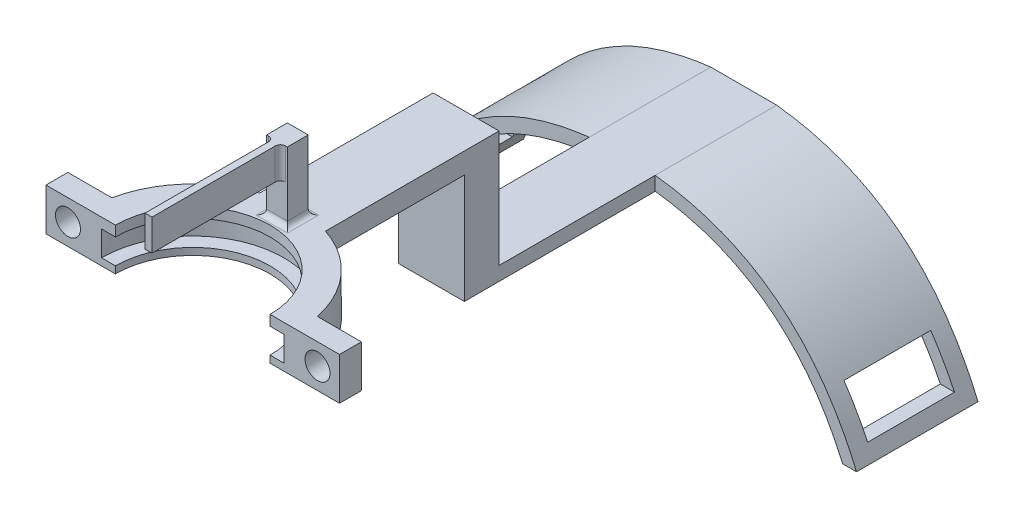
SolidWorks part; units mm, degrees
ref_plane "Front Plane" through (0, 0, 0) normal (0, 0, 1) x (1, 0, 0)
ref_plane "Top Plane" through (0, 0, 0) normal (0, 1, 0) x (1, 0, 0)
ref_plane "Right Plane" through (0, 0, 0) normal (1, 0, 0) x (0, 0, -1)
sketch "Sketch3" plane through (0, 0, 0) normal (0, 0, 1) x (1, 0, 0)
  line L2 (-62.6943, 11.7337) -> (-64.8845, 11.7337)
  line L3 (-62.8845, 10.2507) -> (-60.8845, 10.2507)
  line L5 (-60.8845, 6.6507) -> (-62.8845, 6.6507)
  line L6 (-62.8845, 6.6507) -> (-62.8845, 10.2507)
  line L10 (-64.8845, 11.7337) -> (-64.8845, 5.6398)
  line L11 (-64.8845, 5.6398) -> (-60.8845, 5.6398)
  line L12 (-60.8845, 5.6398) -> (-60.8845, 6.6507)
  line L13 (-60.8845, 10.2507) -> (-60.8845, 11.7337)
  line L14 (-60.8845, 11.7337) -> (-62.6943, 11.7337)
  dimension "D2" = 2
  dimension "D3" = 4
  dimension "D1" = 2
sketch "Sketch4" plane through (0, 0, 0) normal (0, 0, 1) x (1, 0, 0)
  line L0 (-49.7443, 0) -> (-49.7443, 12.8648) construction
  line L1 (27.6543, 0) -> (-27.6543, 0) construction
revolve "Revolve1" add sketch "Sketch3" angle 360 about L0
sketch "Sketch7" plane through (0, 11.7337, 0) normal (0, 1, 0) x (1, 0, 0)
  line L2 (-50.2443, 15.132) -> (-50.2443, 13.1308)
  line L3 (-49.2443, 15.132) -> (-49.2443, 13.1308)
  circle A0 centre (-49.7443, 0) radius 15.1403 construction
  arc A1 (-49.2443, 15.132) -> (-50.2443, 15.132) centre (-49.7443, 0) ccw
  circle A2 centre (-49.7443, 0) radius 13.1403 construction
  arc A3 (-49.2443, 13.1308) -> (-50.2443, 13.1308) centre (-49.7443, 0) ccw
  point P9 (-49.7443, 14.131)
  dimension "D1" = 1
extrude "Boss-Extrude1" add sketch "Sketch7" along normal blind 8.5
sketch "Sketch8" plane through (0, 20.2337, 0) normal (0, 1, 0) x (1, 0, 0)
  line L0 (-50.2443, 15.132) -> (-50.2443, 13.1308) construction
  line L3 (-50.2443, 15.132) -> (-50.2443, 13.1308)
  line L4 (-49.2443, 13.1308) -> (-49.2443, 15.132) construction
  line L5 (-49.2443, 13.1308) -> (-49.2443, 15.132)
  line L6 (-50.2443, 13.1308) -> (-50.2443, -6.3692)
  line L7 (-50.2443, -6.3692) -> (-49.2443, -6.3692)
  line L8 (-49.2443, -6.3692) -> (-49.2443, 13.1308)
  arc A0 (-49.2443, 15.132) -> (-50.2443, 15.132) centre (-49.7443, 0) ccw construction
  arc A1 (-49.2443, 15.132) -> (-50.2443, 15.132) centre (-49.7443, 0) ccw
  dimension "D1" = 19.5
extrude "Boss-Extrude2" add sketch "Sketch8" against normal blind 3
sketch "Sketch9" plane through (0, 11.7337, 0) normal (0, 1, 0) x (1, 0, 0)
  line L2 (-54.4943, 14.3759) -> (-54.4943, 39.3759)
  line L3 (-54.4943, 39.3759) -> (-44.9943, 39.3759)
  line L4 (-44.9943, 39.3759) -> (-44.9943, 14.3759)
  arc A0 (-50.2443, 15.132) -> (-49.2443, 15.132) centre (-49.7443, 0) ccw construction
  arc A1 (-50.2443, 15.132) -> (-54.4943, 14.3759) centre (-49.7443, 0) ccw
  arc A2 (-49.2443, 15.132) -> (-50.2443, 15.132) centre (-49.7443, 0) ccw construction
  arc A3 (-49.2443, 15.132) -> (-50.2443, 15.132) centre (-49.7443, 0) ccw
  arc A4 (-44.9943, 14.3759) -> (-49.2443, 15.132) centre (-49.7443, 0) ccw
  point P9 (-49.7443, 0)
  dimension "D1" = 25
extrude "Boss-Extrude3" add sketch "Sketch9" against normal blind 3
sketch "Sketch10" plane through (0, 8.7337, 0) normal (0, -1, 0) x (1, 0, 0)
  line L0 (-44.9943, -14.3759) -> (-44.9943, -39.3759) construction
  line L1 (-54.4943, -39.3759) -> (-44.9943, -39.3759)
  line L2 (-54.4943, -39.3759) -> (-54.4943, -34.3759)
  line L3 (-54.4943, -34.3759) -> (-44.9943, -34.3759)
  line L4 (-44.9943, -39.3759) -> (-44.9943, -34.3759)
  dimension "D1" = 5
extrude "Boss-Extrude4" add sketch "Sketch10" along normal blind 15.78
sketch "Sketch11" plane through (0, 0, -39.3759) normal (0, 0, -1) x (-1, 0, 0)
  line L0 (54.4943, -7.0463) -> (54.4943, 11.7337) construction
  line L1 (44.9943, -7.0463) -> (54.4943, -7.0463)
  line L2 (44.9943, -7.0463) -> (44.9943, -5.0463)
  line L3 (44.9943, -5.0463) -> (54.4943, -5.0463)
  line L4 (54.4943, -7.0463) -> (54.4943, -5.0463)
  dimension "D1" = 2
extrude "Boss-Extrude5" add sketch "Sketch11" along normal blind 40
sketch "Sketch13" plane through (0, 11.7337, 0) normal (0, 1, 0) x (1, 0, 0)
  line L2 (-49.7443, 3.15) -> (-49.7443, -3.15) construction
  line L3 (-28.604, 3.15) -> (-34.9353, 3.15)
  line L4 (-70.8845, 3.15) -> (-70.8845, -3.15)
  line L5 (-70.8845, -3.15) -> (-64.5532, -3.15)
  line L6 (-28.604, -3.15) -> (-28.604, 3.15)
  line L7 (-64.5532, 3.15) -> (-70.8845, 3.15)
  line L8 (-34.9353, -3.15) -> (-28.604, -3.15)
  arc A0 (-54.4943, 14.3759) -> (-44.9943, 14.3759) centre (-49.7443, 0) ccw construction
  arc A1 (-64.5532, 3.15) -> (-64.5532, -3.15) centre (-49.7443, 0) ccw
  arc A2 (-34.9353, -3.15) -> (-34.9353, 3.15) centre (-49.7443, 0) ccw
  point P10 (-49.7443, 0)
  point P13 (-49.7443, 3.15)
  dimension "D1" = 6.3
  dimension "D2" = 6.3
extrude "Boss-Extrude6" add sketch "Sketch13" against normal up to surface (6.0939 mm away) up to face at (-49.7443, 5.6398, -11.1403)
sketch "Sketch14" plane through (0, 0, 3.15) normal (0, 0, 1) x (1, 0, 0)
  line L0 (-70.8845, 11.7337) -> (-64.5532, 5.6398) construction
  line L1 (-28.604, 11.7337) -> (-34.9353, 5.6398) construction
  circle A0 centre (-31.7697, 8.6868) radius 1.8
  circle A1 centre (-67.7189, 8.6868) radius 1.8
  dimension "D1" = 3.6
  dimension "D2" = 3.6
extrude "Cut-Extrude1" cut sketch "Sketch14" against normal up to surface (6.3 mm away) contours A1 | A0 up to face at (-67.7189, 8.6868, -3.15)
sketch "Sketch15" plane through (0, 11.7337, 0) normal (0, 1, 0) x (1, 0, 0)
  line L0 (-70.8845, 0) -> (-23.4421, 0) construction
  line L1 (-70.8845, 3.15) -> (-70.8845, -3.15) construction
  line L2 (-15.004, 0) -> (15.004, 0) construction
  line L4 (-23.4421, 0) -> (-74.5953, 0)
  line L5 (-23.4421, 0) -> (-23.4421, -21.2106)
  line L6 (-23.4421, -21.2106) -> (-74.5953, -21.2106)
  line L7 (-74.5953, 0) -> (-74.5953, -21.2106)
extrude "Cut-Extrude3" cut sketch "Sketch15" against normal through all
sketch "Sketch16" plane through (0, 0, 0) normal (0, 1, 0) x (1, 0, 0)
  line L1 (-54.8883, 5.4174) -> (-45.2843, 5.4174)
  line L2 (-54.8883, 5.4174) -> (-54.8883, -6.4675)
  line L3 (-54.8883, -6.4675) -> (-45.2843, -6.4675)
  line L4 (-45.2843, 5.4174) -> (-45.2843, -6.4675)
sketch "Sketch18" plane through (0, 11.7337, 0) normal (0, 1, 0) x (1, 0, 0)
  line L0 (-50.2443, 15.132) -> (-49.2443, 15.132) construction
  line L1 (-48.2443, 15.132) -> (-51.2443, 15.132)
  line L2 (-51.2443, 15.132) -> (-51.2443, 12.132)
  line L3 (-51.2443, 12.132) -> (-48.2443, 12.132)
  line L4 (-48.2443, 12.132) -> (-48.2443, 15.132)
  point P7 (-49.7443, 15.132)
  dimension "D1" = 3
  dimension "D2" = 3
extrude "Boss-Extrude7" add sketch "Sketch18" along normal up to surface (8.5 mm away)
fillet "Fillet1" radius 0.75 6 edges at (-50.7443, 11.7337, -15.132) (-48.7443, 11.7337, -15.132) (-49.7443, 11.7337, -12.132) (-48.2443, 11.7337, -13.632) (-51.2443, 11.7337, -13.632) (-49.7443, 11.7337, -15.1403)
sketch "Sketch19" plane through (0, 20.2337, 0) normal (0, 1, 0) x (1, 0, 0)
  line L18 (-50.2443, 15.132) -> (-51.2443, 15.132)
  line L19 (-51.2443, 15.132) -> (-51.2443, 12.132)
  line L20 (-51.2443, 12.132) -> (-50.2443, 12.132)
  line L21 (-50.2443, 12.132) -> (-50.2443, -6.3692)
  line L22 (-50.2443, -6.3692) -> (-49.2443, -6.3692)
  line L23 (-49.2443, -6.3692) -> (-49.2443, 12.132)
  line L24 (-49.2443, 12.132) -> (-48.2443, 12.132)
  line L25 (-48.2443, 12.132) -> (-48.2443, 15.132)
  line L26 (-48.2443, 15.132) -> (-49.2443, 15.132)
  line L27 (-50.2443, 15.132) -> (-51.2443, 15.132)
  line L28 (-51.2443, 15.132) -> (-51.2443, 12.132)
  line L29 (-51.2443, 12.132) -> (-50.2443, 12.132)
  line L30 (-50.2443, 12.132) -> (-50.2443, -6.3692)
  line L31 (-50.2443, -6.3692) -> (-49.2443, -6.3692)
  line L32 (-49.2443, -6.3692) -> (-49.2443, 12.132)
  line L33 (-49.2443, 12.132) -> (-48.2443, 12.132)
  line L34 (-48.2443, 12.132) -> (-48.2443, 15.132)
  line L35 (-48.2443, 15.132) -> (-49.2443, 15.132)
  arc A2 (-49.2443, 15.132) -> (-50.2443, 15.132) centre (-49.7443, 0) ccw
  arc A3 (-49.2443, 15.132) -> (-50.2443, 15.132) centre (-49.7443, 0) ccw
  dimension "D1" = 0
extrude "Boss-Extrude8" add sketch "Sketch19" along normal blind 1.5
fillet "Fillet2" radius 0.75 2 edges at (-49.2443, 19.4837, -12.132) (-50.2443, 19.4837, -12.132)
sketch "Sketch20" plane through (0, 0, -79.3759) normal (0, 0, -1) x (-1, 0, 0)
  line L0 (49.7443, -5.0463) -> (49.7443, -27.5463) construction
  line L1 (54.4943, -5.0463) -> (44.9943, -5.0463) construction
  line L2 (83.4943, -27.5463) -> (15.9943, -27.5463) construction
  line L4 (15.9943, -27.5463) -> (17.9943, -27.5463)
  line L5 (81.4943, -27.5463) -> (83.4943, -27.5463)
  line L8 (44.9943, -7.0463) -> (54.4943, -7.0463)
  line L9 (44.9943, -5.0463) -> (54.4943, -5.0463)
  line L11 (54.4943, -5.0463) -> (44.9943, -5.0463) construction
  spline S0 degree 2 poles (15.9943, -27.5463) (24.4754, -7.3884) (44.9943, -5.0463) knots 0 0 0 0.448315 0.448315 0.448315
  spline S1 degree 2 poles (17.9943, -27.5463) (25.8778, -9.3271) (44.9943, -7.0463) knots 0 0 0 0.444959 0.444959 0.444959
  spline S2 degree 2 poles (54.4943, -5.0463) (75.0132, -7.3884) (83.4943, -27.5463) knots 0.551685 0.551685 0.551685 1 1 1
  spline S3 degree 2 poles (54.4943, -7.0463) (73.6108, -9.3271) (81.4943, -27.5463) knots 0.555041 0.555041 0.555041 1 1 1
  point P7 (49.7443, -27.5463)
  dimension "D3" = 2
  dimension "D1" = 22.5
  dimension "D2" = 67.5
  dimension "D4" = 2
extrude "Boss-Extrude9" add sketch "Sketch20" against normal blind 17.5
sketch "Sketch21" plane through (-44.9943, 0, 0) normal (1, 0, 0) x (0, 0, -1)
  line L0 (70.6259, -27.5463) -> (70.6259, -25.5463) construction
  line L1 (61.8759, -27.5463) -> (79.3759, -27.5463) construction
  line L2 (76.8759, -25.5463) -> (64.3759, -25.5463) construction
  line L4 (64.3759, -25.5463) -> (76.8759, -25.5463)
  line L5 (64.3759, -25.5463) -> (64.3759, -19.5463)
  line L6 (64.3759, -19.5463) -> (76.8759, -19.5463)
  line L7 (76.8759, -25.5463) -> (76.8759, -19.5463)
  point P7 (70.6259, -25.5463)
  dimension "D1" = 6
  dimension "D2" = 2
extrude "Cut-Extrude4" cut sketch "Sketch21" against normal through all both and the other way through all
